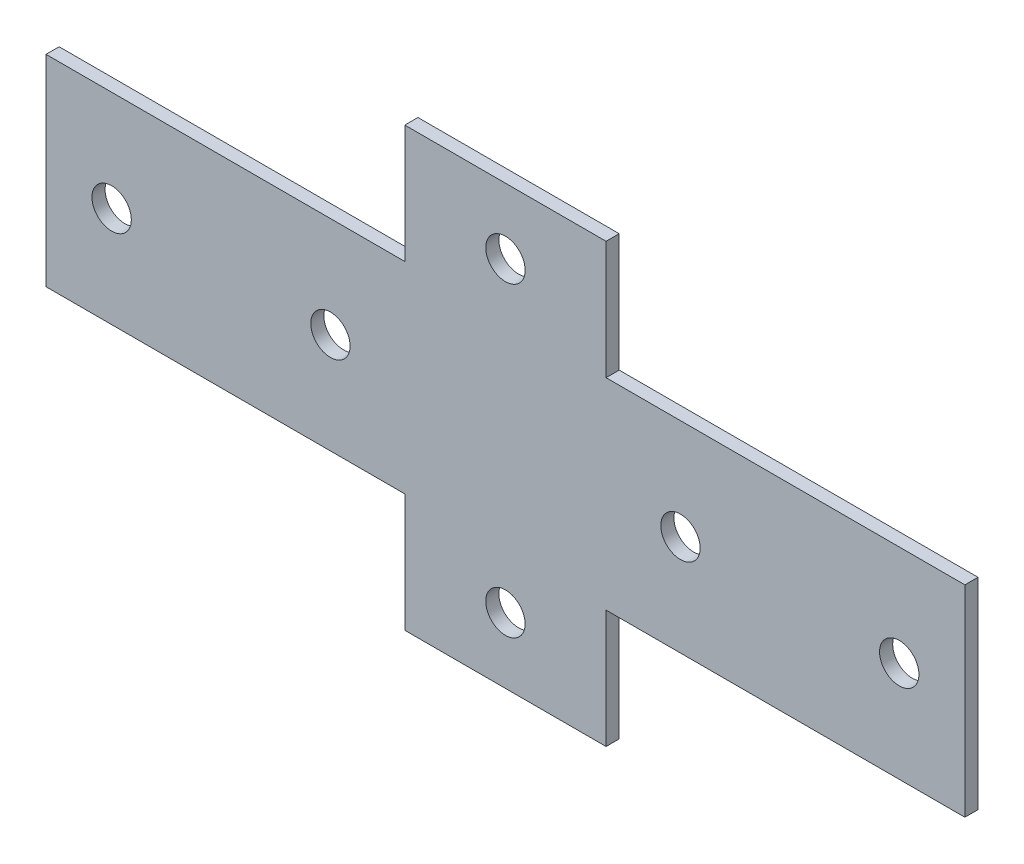
SolidWorks part; units mm, degrees
ref_plane "Спереди" through (0, 0, 0) normal (0, 0, 1) x (1, 0, 0)
ref_plane "Сверху" through (0, 0, 0) normal (0, 1, 0) x (1, 0, 0)
ref_plane "Справа" through (0, 0, 0) normal (1, 0, 0) x (0, 0, -1)
sketch "Эскиз1" plane through (0, 0, 0) normal (0, 0, 1) x (1, 0, 0)
  line L0 (23, -23) -> (105, -23)
  line L1 (-105, 23) -> (-23, 23)
  line L2 (-105, 23) -> (-105, -23)
  line L3 (-105, -23) -> (-23, -23)
  line L4 (105, 23) -> (105, -23)
  line L5 (-105, 23) -> (105, -23) construction
  line L6 (-105, -23) -> (105, 23) construction
  line L7 (-23, -50) -> (23, -50)
  line L8 (-23, -50) -> (-23, -23)
  line L9 (-23, 50) -> (23, 50)
  line L10 (23, -50) -> (23, -23)
  line L11 (-23, -50) -> (23, 50) construction
  line L12 (-23, 50) -> (23, -50) construction
  line L13 (23, 23) -> (105, 23)
  line L14 (-23, 23) -> (-23, 50)
  line L15 (23, 23) -> (23, 50)
  line L16 (0, 35) -> (0, -35) construction
  line L17 (0, 35) -> (0, 50) construction
  line L18 (-90, 0) -> (-105, 0) construction
  circle A0 centre (0, 35) radius 4.5
  circle A1 centre (0, -35) radius 4.5
  circle A2 centre (-90, 0) radius 4.5
  circle A3 centre (-40, 0) radius 4.5
  circle A4 centre (40, 0) radius 4.5
  circle A5 centre (90, 0) radius 4.5
  point P0 (0, 0)
  point P6 (0, 0)
  dimension "D4" = 15
  dimension "D5" = 9
  dimension "D6" = 50
  dimension "D1" = 210
  dimension "D2" = 100
  dimension "D3" = 46
extrude "Бобышка-Вытянуть1" add sketch "Эскиз1" along normal blind 3
